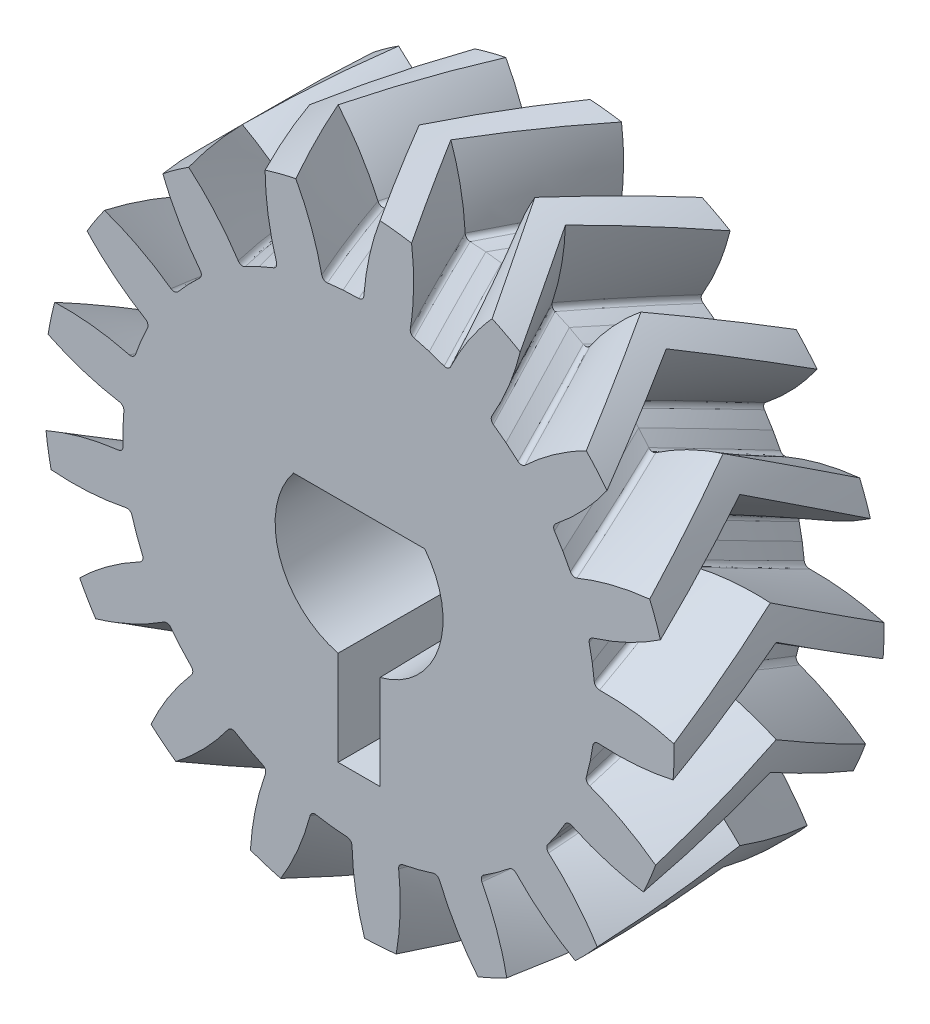
SolidWorks part; units mm, degrees
ref_plane "Front Plane" through (0, 0, 0) normal (0, 0, 1) x (1, 0, 0)
ref_plane "Top Plane" through (0, 0, 0) normal (0, 1, 0) x (1, 0, 0)
ref_plane "Right Plane" through (0, 0, 0) normal (1, 0, 0) x (0, 0, -1)
sketch "Sketch1" plane through (0, 0, 0) normal (0, 0, 1) x (1, 0, 0)
  circle A0 centre (0, 0) radius 6
  dimension "D1" = 12
extrude "Boss-Extrude1" add sketch "Sketch1" along normal blind 2
sketch "Sketch2" plane through (0, 0, 2) normal (0, 0, 1) x (1, 0, 0)
  circle A0 centre (0, 0) radius 6 construction
  circle A1 centre (0, 0) radius 6
curve "Helix/Spiral1" pitch 60 height 3 turns 0.05
sketch "Sketch3" plane through (0, 0, 2) normal (0, 0, 1) x (1, 0, 0)
  line L0 (0, 0) -> (7.7063, 0) construction
  line L1 (4.5, 0) -> (4.49, 0.3)
  line L2 (6.5, 1.1) -> (6.5, -1.1)
  line L3 (4.5, 0) -> (4.49, -0.3)
  circle A0 centre (0, 0) radius 4.5 construction
  arc A1 (4.49, 0.3) -> (4.5758, 0.4023) centre (4.5899, 0.3033) cw
  arc A2 (4.5758, 0.4023) -> (6.5, 1.1) centre (3.8697, 5.3522) ccw
  arc A3 (4.5758, -0.4023) -> (6.5, -1.1) centre (3.8697, -5.3522) cw
  arc A4 (4.49, -0.3) -> (4.5758, -0.4023) centre (4.5899, -0.3033) ccw
  point P16 (6.5, 0)
  dimension "D1" = 9
  dimension "D5" = 0.1
  dimension "D6" = 5
  dimension "D2" = 2
  dimension "D3" = 0.3
  dimension "D4" = 1.1
sweep "Cut-Sweep1" cut profiles "Sketch3" path "Helix/Spiral1"
pattern_circular "CirPattern1" count 17 over 360 about axis through (0, 0, 2) along (0, 0, 1) of "Cut-Sweep1"
mirror "Mirror1" about plane through (0, 0, 2) normal (0, 0, 1)
sketch "Sketch4" plane through (0, 0, 4) normal (0, 0, 1) x (1, 0, 0)
  line L0 (-1.25, 0.9987) -> (1.25, 0.9987)
  line L1 (0.4, -1.5492) -> (0.4, -3.3492)
  line L2 (0.4, -3.3492) -> (-0.4, -3.3492)
  line L3 (-0.4, -3.3492) -> (-0.4, -1.5492)
  arc A0 (-1.25, 0.9987) -> (-0.4, -1.5492) centre (0, 0) ccw
  arc A1 (0.4, -1.5492) -> (1.25, 0.9987) centre (0, 0) ccw
  dimension "D1" = 1.6
  dimension "D2" = 2.5
  dimension "D3" = 1.8
  dimension "D4" = 0.8
extrude "Cut-Extrude1" cut sketch "Sketch4" against normal through all draft 0.75
